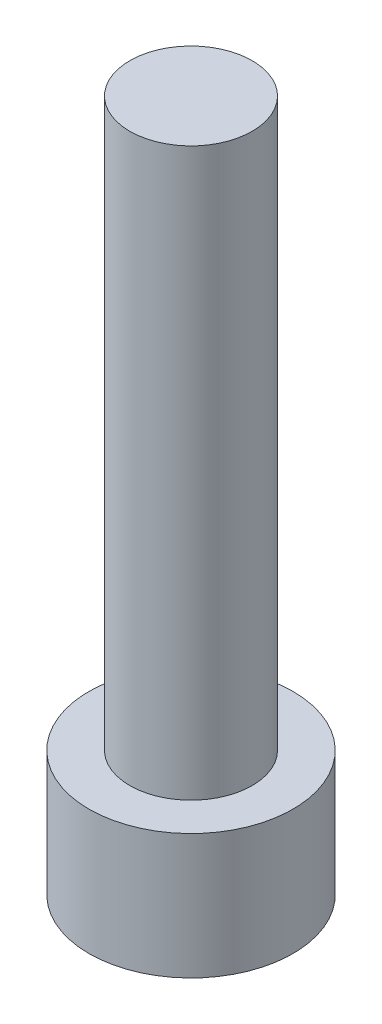
SolidWorks part; units mm, degrees
ref_plane "Front Plane" through (0, 0, 0) normal (0, 0, 1) x (1, 0, 0)
ref_plane "Top Plane" through (0, 0, 0) normal (0, 1, 0) x (1, 0, 0)
ref_plane "Right Plane" through (0, 0, 0) normal (1, 0, 0) x (0, 0, -1)
sketch "Sketch1" plane through (0, 0, 0) normal (0, 1, 0) x (1, 0, 0)
  circle A0 centre (0, 0) radius 2.8575
  dimension "D1" = 5.715
extrude "Boss-Extrude1" add sketch "Sketch1" along normal blind 3.5052
sketch "Sketch2" plane through (0, 0, 0) normal (0, -1, 0) x (1, 0, 0)
  line L1 (1.604, 0) -> (0.802, 1.3891)
  line L2 (0.802, 1.3891) -> (-0.802, 1.3891)
  line L3 (-0.802, 1.3891) -> (-1.604, 0)
  line L4 (-1.604, 0) -> (-0.802, -1.3891)
  line L5 (-0.802, -1.3891) -> (0.802, -1.3891)
  line L6 (0.802, -1.3891) -> (1.604, 0)
  circle A0 centre (0, 0) radius 1.3891 construction
  dimension "D1" = 2.7781
extrude "Cut-Extrude1" cut sketch "Sketch2" against normal blind 1.9558
sketch "Sketch3" plane through (0, 3.5052, 0) normal (0, 1, 0) x (1, 0, 0)
  circle A0 centre (0, 0) radius 1.7145
  dimension "D1" = 3.429
extrude "Boss-Extrude2" add sketch "Sketch3" along normal blind 15.875
